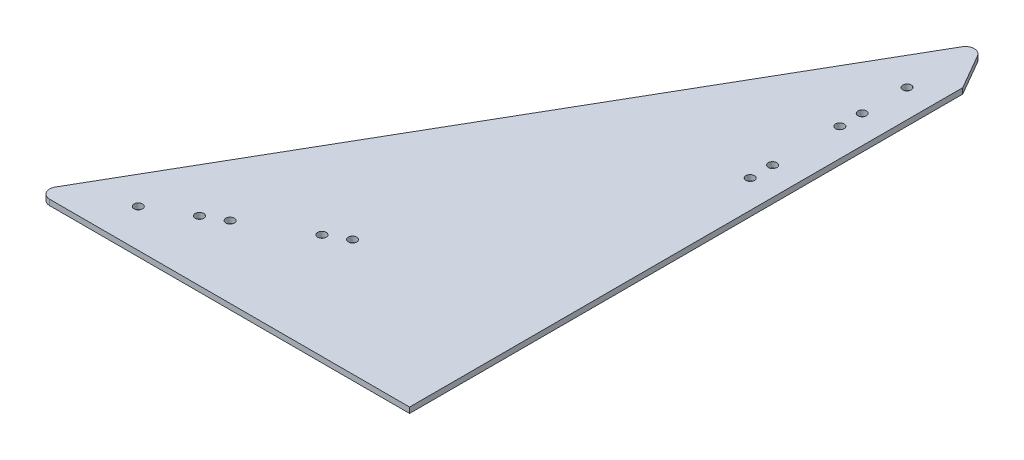
SolidWorks part; units mm, degrees
ref_plane "Front Plane" through (0, 0, 0) normal (0, 0, 1) x (1, 0, 0)
ref_plane "Top Plane" through (0, 0, 0) normal (0, 1, 0) x (1, 0, 0)
ref_plane "Right Plane" through (0, 0, 0) normal (1, 0, 0) x (0, 0, -1)
sketch "Sketch1" plane through (0, 0, 0) normal (0, 1, 0) x (1, 0, 0)
  line L0 (0, 0) -> (393.7, 0)
  line L1 (393.7, 0) -> (196.85, 340.9542)
  line L2 (196.85, 340.9542) -> (0, 0)
  dimension "D1" = 393.7
extrude "Boss-Extrude1" add sketch "Sketch1" along normal blind 3.175
fillet "Fillet1" radius 5.08 3 edges at (196.85, 1.5875, -340.9542) (393.7, 1.5875, 0) (0, 1.5875, 0)
sketch "Sketch2" plane through (0, 3.175, 0) normal (0, 1, 0) x (1, 0, 0)
  line L0 (4.3994, 2.54) -> (295.275, 170.4771) construction
  line L1 (389.3006, 7.62) -> (201.2494, 333.3342) construction
  line L2 (389.3006, 2.54) -> (98.425, 170.4771) construction
  line L3 (192.4506, 333.3342) -> (4.3994, 7.62) construction
  line L4 (196.85, 335.8742) -> (196.85, 0) construction
  line L5 (8.7988, 0) -> (384.9012, 0) construction
  arc A0 (4.3994, 7.62) -> (8.7988, 0) centre (8.7988, 5.08) ccw construction
  arc A1 (384.9012, 0) -> (389.3006, 7.62) centre (384.9012, 5.08) ccw construction
  arc A2 (201.2494, 333.3342) -> (192.4506, 333.3342) centre (196.85, 330.7942) ccw construction
  circle A8 centre (37.395, 21.59) radius 2.413
  circle A10 centre (59.392, 34.29) radius 2.413
  circle A11 centre (70.3905, 40.64) radius 2.413
  circle A13 centre (114.3846, 66.04) radius 2.413
  circle A14 centre (103.3861, 59.69) radius 2.413
  circle A17 centre (196.85, 297.7742) radius 2.413
  circle A19 centre (196.85, 272.3742) radius 2.413
  circle A20 centre (196.85, 259.6742) radius 2.413
  circle A23 centre (196.85, 221.5742) radius 2.413
  circle A24 centre (196.85, 208.8742) radius 2.413
  circle A25 centre (279.3154, 66.04) radius 2.413
  circle A26 centre (290.3139, 59.69) radius 2.413
  circle A29 centre (323.3095, 40.64) radius 2.413
  circle A30 centre (334.308, 34.29) radius 2.413
  circle A32 centre (356.305, 21.59) radius 2.413
  dimension "D3" = 4.826
  dimension "D8" = 25.4
  dimension "D2" = 38.1
  dimension "D4" = 25.4
  dimension "D5" = 38.1
  dimension "D6" = 12.7
  dimension "D7" = 38.1
  dimension "D9" = 12.7
  dimension "D10" = 12.7
  dimension "D11" = 38.1
  dimension "D12" = 12.7
extrude "Cut-Extrude1" cut sketch "Sketch2" against normal up to surface (3.175 mm away) up to face at (196.85, 0, -113.6514)
sketch "Sketch3" plane through (0, 3.175, 0) normal (0, 1, 0) x (1, 0, 0)
  line L0 (212.725, 313.4579) -> (212.725, 0)
  line L1 (389.3006, 7.62) -> (201.2494, 333.3342) construction
  line L2 (8.7988, 0) -> (384.9012, 0) construction
  line L3 (196.85, 340.9542) -> (196.85, 0)
  line L4 (0, 0) -> (393.7, 0) construction
  line L8 (389.3006, 7.62) -> (201.2494, 333.3342)
  line L9 (192.4506, 333.3342) -> (4.3994, 7.62)
  line L10 (8.7988, 0) -> (384.9012, 0)
  line L11 (389.3006, 7.62) -> (201.2494, 333.3342)
  line L12 (192.4506, 333.3342) -> (4.3994, 7.62)
  line L13 (8.7988, 0) -> (384.9012, 0)
  arc A3 (201.2494, 333.3342) -> (192.4506, 333.3342) centre (196.85, 330.7942) ccw
  arc A4 (4.3994, 7.62) -> (8.7988, 0) centre (8.7988, 5.08) ccw
  arc A5 (384.9012, 0) -> (389.3006, 7.62) centre (384.9012, 5.08) ccw
  arc A6 (201.2494, 333.3342) -> (192.4506, 333.3342) centre (196.85, 330.7942) ccw
  arc A7 (4.3994, 7.62) -> (8.7988, 0) centre (8.7988, 5.08) ccw
  arc A8 (384.9012, 0) -> (389.3006, 7.62) centre (384.9012, 5.08) ccw
  circle M4 centre (356.305, 21.59) radius 2.413
  circle M5 centre (334.308, 34.29) radius 2.413
  circle M6 centre (323.3095, 40.64) radius 2.413
  circle M7 centre (290.3139, 59.69) radius 2.413
  circle M8 centre (279.3154, 66.04) radius 2.413
  line M18 (389.3006, 7.62) -> (201.2494, 333.3342)
  line M22 (8.7988, 0) -> (384.9012, 0)
  arc M23 (384.9012, 0) -> (389.3006, 7.62) centre (384.9012, 5.08) ccw
  dimension "D1" = 15.875
  dimension "D2" = 0
extrude "Cut-Extrude2" cut sketch "Sketch3" against normal up to surface (3.175 mm away) contours L0 M18 M22 M23 M5 M7 M8 M6 M4 up to face at (37.395, 0, -19.177)
